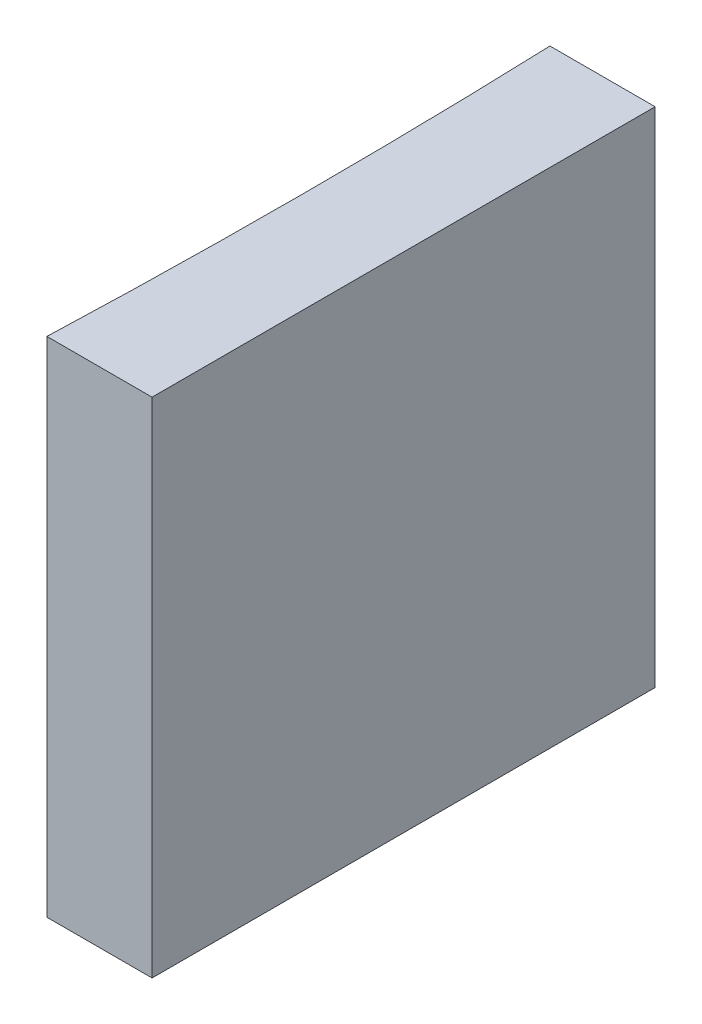
SolidWorks part; units mm, degrees
ref_plane "前视基准面" through (0, 0, 0) normal (0, 0, 1) x (1, 0, 0)
ref_plane "上视基准面" through (0, 0, 0) normal (0, 1, 0) x (1, 0, 0)
ref_plane "右视基准面" through (0, 0, 0) normal (1, 0, 0) x (0, 0, -1)
sketch "草图1" plane through (0, 0, 0) normal (0, 1, 0) x (1, 0, 0)
  line L0 (0, 0) -> (0, -10)
  line L1 (0, 0) -> (-2.0909, 0)
  line L2 (0, -10) -> (-2.0909, -10)
  line L3 (21.2259, -5) -> (-21.2259, -5) construction
  arc A0 (-2.0909, -10) -> (-2.0909, 0) centre (-139.55, -5) ccw
  point P7 (-2, -5)
  point P8 (0, -5)
  dimension "D2" = 137.55
  dimension "D3" = 2
  dimension "D1" = 10
extrude "凸台-拉伸1" add sketch "草图1" along normal blind 10
